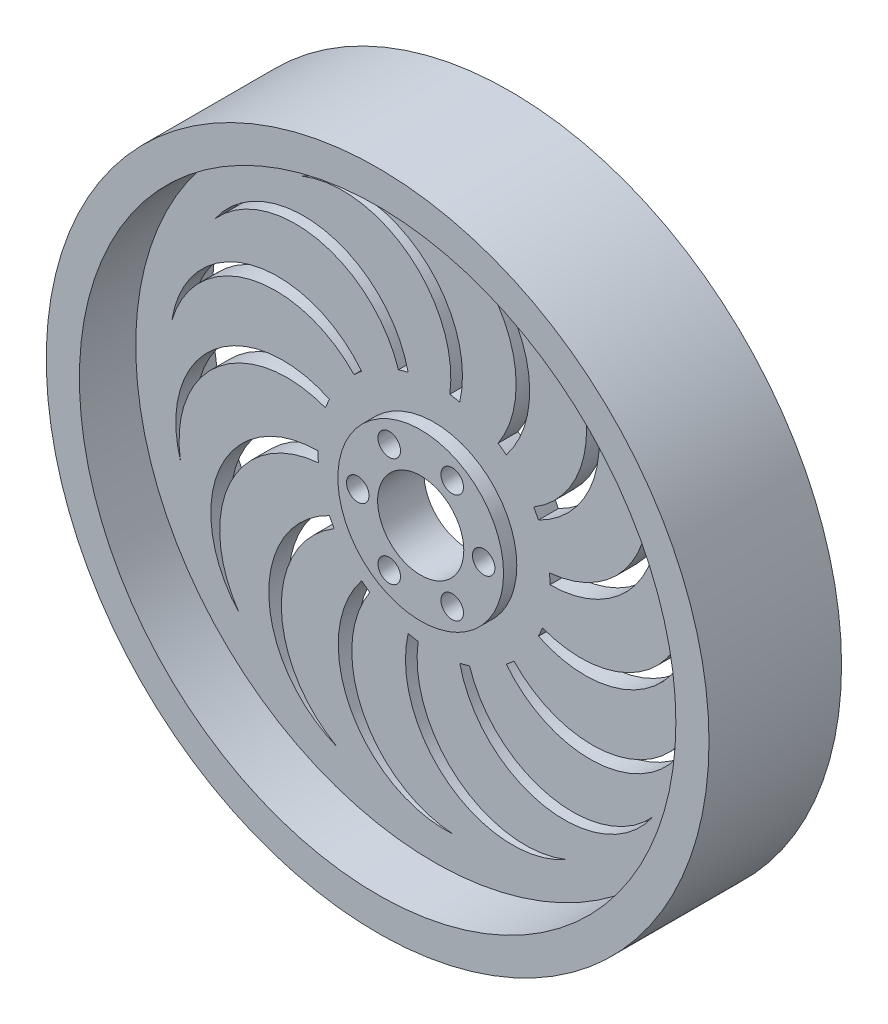
SolidWorks part; units mm, degrees
ref_plane "Front Plane" through (0, 0, 0) normal (0, 0, 1) x (1, 0, 0)
ref_plane "Top Plane" through (0, 0, 0) normal (0, 1, 0) x (1, 0, 0)
ref_plane "Right Plane" through (0, 0, 0) normal (1, 0, 0) x (0, 0, -1)
sketch "Sketch1" plane through (0, 0, 0) normal (0, 1, 0) x (1, 0, 0)
  line L0 (0, -77.7422) -> (0, 81.729) construction
  line L1 (9.5, 19.6041) -> (9.5, -23.4618) construction
  line L2 (6.5, -3.5) -> (12.5, -3.5)
  line L3 (6.5, -3.5) -> (6.5, 3.5)
  line L4 (6.5, 3.5) -> (12.5, 3.5)
  line L5 (12.5, -3.5) -> (12.5, 3.5)
  line L6 (6.5, -3.5) -> (12.5, 3.5) construction
  line L7 (6.5, 3.5) -> (12.5, -3.5) construction
  line L8 (45, -1.5) -> (12.5, -1.5)
  line L9 (45, -1.5) -> (45, 1.5)
  line L10 (45, 1.5) -> (12.5, 1.5)
  line L11 (12.5, -1.5) -> (12.5, 1.5)
  line L12 (45, -1.5) -> (12.5, 1.5) construction
  line L13 (45, 1.5) -> (12.5, -1.5) construction
  line L14 (50, -10) -> (45, -10)
  line L15 (50, -10) -> (50, 10)
  line L16 (50, 10) -> (45, 10)
  line L17 (45, -10) -> (45, 10)
  line L18 (50, -10) -> (45, 10) construction
  line L19 (50, 10) -> (45, -10) construction
  point P2 (9.5, 0)
  point P8 (28.75, 0)
  point P13 (47.5, 0)
  point P18 (0, 0)
  dimension "D1" = 6
  dimension "D3" = 5
  dimension "D4" = 100
  dimension "D5" = 7
  dimension "D6" = 3
  dimension "D7" = 20
  dimension "D8" = 9.5
revolve "Revolve1" add sketch "Sketch1" angle 360 about L0
sketch "Sketch2" plane through (0, 0, 3.5) normal (0, 0, 1) x (1, 0, 0)
  line L0 (0, 0) -> (12.5, 0) construction
  circle A0 centre (0, 0) radius 12.5 construction
  point P6 (9.5, 0)
  point P7 (4.75, -8.2272)
  point P10 (-4.75, -8.2272)
  point P11 (-9.5, 0)
  point P12 (-4.75, 8.2272)
  point P13 (4.75, 8.2272)
  point P14 (0, 0)
  dimension "D1" = 9.5
  dimension "D2" = 6
hole_wizard "M3 Clearance Hole1" positions "Sketch3" profile "Sketch4" hole size "M3" standard "ANSI Metric" end condition through all
sketch "Sketch3" plane through (0, 0, 3.5) normal (0, 0, 1) x (1, 0, 0)
  point P0 (-4.75, 8.2272)
  point P3 (4.75, 8.2272)
  point P6 (9.5, 0)
  point P9 (4.75, -8.2272)
  point P12 (-4.75, -8.2272)
  point P15 (-9.5, 0)
sketch "Sketch4" plane through (-4.75, 8.2272, 3.5) normal (1, 0, 0) x (0, -1, 0)
  line L0 (0, 0) -> (0, 13.5)
  line L1 (0, 13.5) -> (1.7, 13.5)
  line L2 (1.7, 13.5) -> (1.7, 0)
  line L5 (1.7, 0) -> (0, 0)
  line L11 (0, -6.35) -> (0, 107.95) construction
  dimension "Thru Hole Dia." = 3.4
  dimension "Thru Hole Depth" = 13.5
sketch "Sketch5" plane through (0, 0, 1.5) normal (0, 0, 1) x (1, 0, 0)
  line L0 (0, 0) -> (45, 0) construction
  line L1 (0, 0) -> (44.8288, 3.922) construction
  circle A0 centre (0, 0) radius 45 construction
  circle A1 centre (0, 0) radius 17.5
  circle A2 centre (0, 0) radius 12.5 construction
  circle A3 centre (0, 0) radius 40
  arc A4 (17.5, 0) -> (29.377, 27.1475) centre (17.5, 16.1719) ccw
  circle A5 centre (0, 0) radius 45 construction
  arc A6 (17.4334, 1.5252) -> (29.377, 27.1475) centre (16.011, 17.7831) ccw
  point P19 (0, 0)
  point P20 (0, 0)
  point P21 (0, 0)
  point P22 (28.923, 27.6307)
  dimension "D1" = 5
  dimension "D2" = 5
  dimension "D3" = 5
extrude "Cut-Extrude1" cut sketch "Sketch5" against normal through all contours A6 A1 A4
pattern_circular "CirPattern1" count 14 over 360 about axis through (0, 0, 0) along (0, 0, 1) of "Cut-Extrude1"
